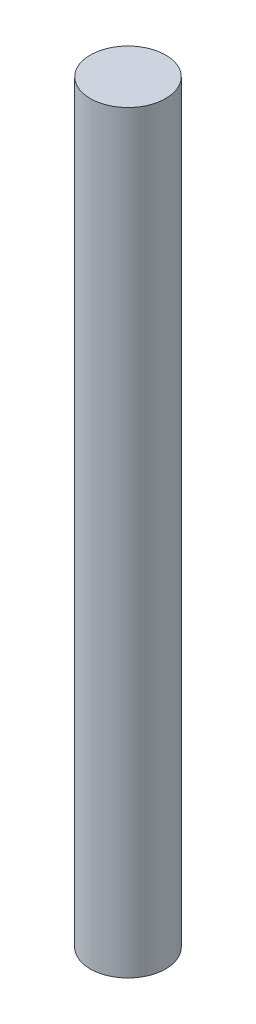
SolidWorks part; units mm, degrees
ref_plane "Front Plane" through (0, 0, 0) normal (0, 0, 1) x (1, 0, 0)
ref_plane "Top Plane" through (0, 0, 0) normal (0, 1, 0) x (1, 0, 0)
ref_plane "Right Plane" through (0, 0, 0) normal (1, 0, 0) x (0, 0, -1)
ref_plane "Plane1" through (0, 0, 0) normal (0, 0, -1) x (-1, 0, 0)
sketch "Sketch1" plane through (0, 0, 0) normal (0, 0, -1) x (-1, 0, 0)
  line L0 (-26.25, 0) -> (0, 0)
  line L1 (0, 0) -> (0, 525)
  line L2 (0, 525) -> (-26.25, 525)
  line L3 (-26.25, 525) -> (-26.25, 0)
  line L4 (0, 0) -> (0, 525) construction
revolve "Revolve1" add sketch "Sketch1" angle 360 about L4
